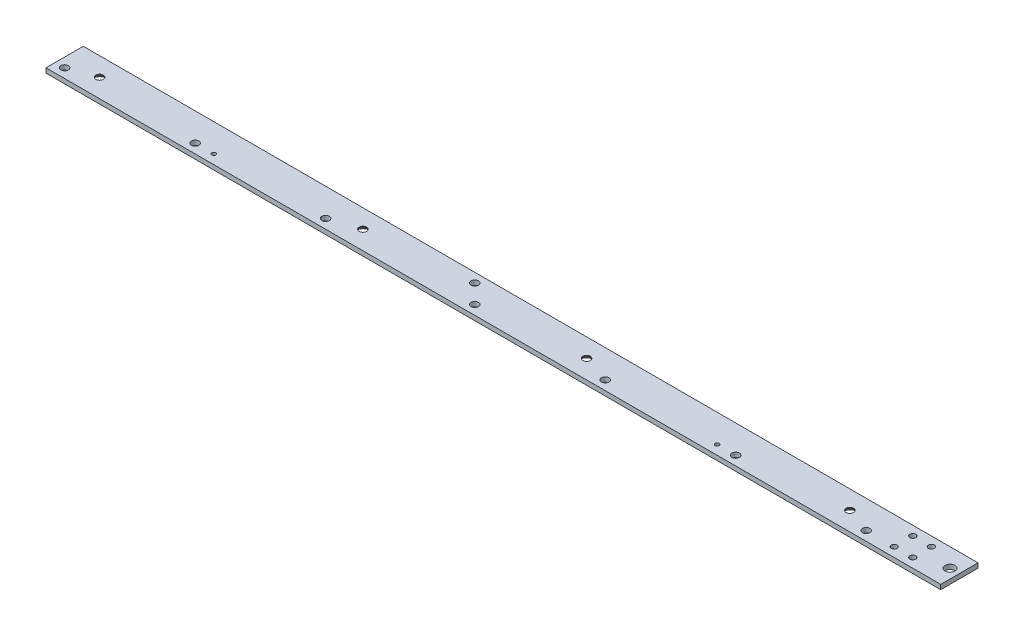
SolidWorks part; units mm, degrees
material "Copper"
ref_plane "Front Plane" through (0, 0, 0) normal (0, 0, 1) x (1, 0, 0)
ref_plane "Top Plane" through (0, 0, 0) normal (0, 1, 0) x (1, 0, 0)
ref_plane "Right Plane" through (0, 0, 0) normal (1, 0, 0) x (0, 0, -1)
sketch "Sketch1" plane through (0, 0, 0) normal (1, 0, 0) x (0, 0, -1)
  line L1 (-12.7, 1.5875) -> (12.7, 1.5875)
  line L2 (-12.7, 1.5875) -> (-12.7, -1.5875)
  line L3 (-12.7, -1.5875) -> (12.7, -1.5875)
  line L4 (12.7, 1.5875) -> (12.7, -1.5875)
  line L5 (-12.7, 1.5875) -> (12.7, -1.5875) construction
  line L6 (-12.7, -1.5875) -> (12.7, 1.5875) construction
  point P0 (0, 0)
  dimension "D1" = 3.175
  dimension "D2" = 25.4
extrude "Boss-Extrude1" add sketch "Sketch1" along normal mid plane 558.8
hole_wizard "#10 Clearance Hole1" positions "Sketch2" profile "Sketch3" hole size "#10" standard "ANSI Inch" end condition through all
sketch "Sketch2" plane through (0, 1.5875, 0) normal (0, 1, 0) x (1, 0, 0)
  line L0 (279.4, -12.7) -> (-279.4, -12.7) construction
  line L1 (-279.4, 12.7) -> (-279.4, -12.7) construction
  point P0 (-273.05, -6.35)
  point P2 (-184.15, -6.35)
  point P4 (-95.25, -6.35)
  dimension "D1" = 6.35
  dimension "D2" = 88.9
  dimension "D3" = 88.9
  dimension "D4" = 6.35
sketch "Sketch3" plane through (-273.05, 1.5875, 6.35) normal (1, 0, 0) x (0, 0, 1)
  line L0 (0, 0) -> (0, 3.175)
  line L1 (0, 3.175) -> (2.5527, 3.175)
  line L2 (2.5527, 3.175) -> (2.5527, 0)
  line L5 (2.5527, 0) -> (0, 0)
  line L11 (0, -6.35) -> (0, 107.95) construction
  dimension "Thru Hole Dia." = 5.1054
  dimension "Thru Hole Depth" = 3.175
hole_wizard "CSK for #10 Flat Head Machine Screw1" positions "Sketch4" profile "Sketch5" countersink size "#10" standard "ANSI Inch" end condition through all
sketch "Sketch4" plane through (0, -1.5875, 0) normal (0, -1, 0) x (-1, 0, 0)
  circle A0 centre (273.05, -6.35) radius 2.5527 construction
  circle A1 centre (95.25, -6.35) radius 2.5527 construction
  point P0 (255.5875, 0)
  point P2 (76.2, 0)
  dimension "D2" = 19.05
  dimension "D1" = 17.4625
sketch "Sketch5" plane through (-255.5875, -1.5875, 0) normal (1, 0, 0) x (0, 0, -1)
  line L0 (0, 0) -> (0, 3.175)
  line L1 (0, 3.175) -> (2.5527, 3.175)
  line L2 (2.5527, 3.175) -> (2.5527, 2.6882)
  line L3 (2.5527, 2.6882) -> (4.8895, 0)
  line L5 (4.8895, 0) -> (0, 0)
  line L6 (-2.5527, 2.6882) -> (-4.8895, 0) construction
  line L11 (0, -6.35) -> (0, 107.95) construction
  dimension "Thru Hole Dia." = 5.1054
  dimension "Thru Hole Depth" = 3.175
  dimension "Near C'Sink Dia." = 9.779
  dimension "Near C'Sink Angle" = 82
hole_wizard "#6-32 Tapped Hole1" positions "Sketch8" profile "Sketch9" tap size "#6-32" standard "ANSI Inch" end condition through all
sketch "Sketch8" plane through (0, 1.5875, 0) normal (0, 1, 0) x (1, 0, 0)
  line L0 (279.4, -12.7) -> (-279.4, -12.7) construction
  circle A0 centre (-184.15, -6.35) radius 2.5527 construction
  point P0 (-171.45, -6.35)
  dimension "D1" = 6.35
  dimension "D2" = 12.7
sketch "Sketch9" plane through (-171.45, 1.5875, 6.35) normal (1, 0, 0) x (0, 0, 1)
  line L0 (0, 0) -> (0, 3.175)
  line L1 (0, 3.175) -> (1.3525, 3.175)
  line L2 (1.3525, 3.175) -> (1.3525, 0)
  line L5 (1.3525, 0) -> (0, 0)
  line L11 (0, -6.35) -> (0, 107.95) construction
  dimension "Thru Tap Drill Dia." = 2.7051
  dimension "Thru Tap Drill Depth" = 3.175
cosmetic thread "Hole Thread1" parameters "D2"=3.5052
mirror "Mirror1" about plane through (0, 0, 0) normal (1, 0, 0) of "#6-32 Tapped Hole1", "#10 Clearance Hole1", "CSK for #10 Flat Head Machine Screw1"
hole_wizard "#10 Clearance Hole2" positions "Sketch10" profile "Sketch11" hole size "#10" standard "ANSI Inch" end condition through all
sketch "Sketch10" plane through (0, 1.5875, 0) normal (0, 1, 0) x (1, 0, 0)
  point P0 (-6.35, 6.35)
  point P2 (6.35, -6.35)
  dimension "D1" = 6.35
  dimension "D2" = 6.35
  dimension "D3" = 6.35
  dimension "D4" = 6.35
sketch "Sketch11" plane through (-6.35, 1.5875, -6.35) normal (1, 0, 0) x (0, 0, 1)
  line L0 (0, 0) -> (0, 3.175)
  line L1 (0, 3.175) -> (2.5527, 3.175)
  line L2 (2.5527, 3.175) -> (2.5527, 0)
  line L5 (2.5527, 0) -> (0, 0)
  line L11 (0, -6.35) -> (0, 107.95) construction
  dimension "Thru Hole Dia." = 5.1054
  dimension "Thru Hole Depth" = 3.175
sketch "Sketch12" plane through (279.4, 0, 0) normal (1, 0, 0) x (0, 0, -1)
  line L0 (-12.7, 1.5875) -> (-12.7, -1.5875) construction
  line L1 (-12.7, -1.5875) -> (12.7, -1.5875) construction
  line L2 (12.7, -1.5875) -> (12.7, 1.5875) construction
  line L3 (12.7, 1.5875) -> (-12.7, 1.5875) construction
  line L4 (-12.7, 1.5875) -> (-12.7, -1.5875)
  line L5 (-12.7, -1.5875) -> (12.7, -1.5875)
  line L6 (12.7, -1.5875) -> (12.7, 1.5875)
  line L7 (12.7, 1.5875) -> (-12.7, 1.5875)
extrude "Boss-Extrude2" add sketch "Sketch12" along normal blind 50.8
hole_wizard "1/4 Clearance Hole1" positions "Sketch13" profile "Sketch14" hole size "1/4" standard "ANSI Inch" end condition through all
sketch "Sketch13" plane through (0, 1.5875, 0) normal (0, 1, 0) x (1, 0, 0)
  line L0 (330.2, 12.7) -> (330.2, -12.7) construction
  point P0 (323.85, 0)
  dimension "D1" = 6.35
sketch "Sketch14" plane through (323.85, 1.5875, 0) normal (1, 0, 0) x (0, 0, 1)
  line L0 (0, 0) -> (0, 3.175)
  line L1 (0, 3.175) -> (3.3782, 3.175)
  line L2 (3.3782, 3.175) -> (3.3782, 0)
  line L5 (3.3782, 0) -> (0, 0)
  line L11 (0, -6.35) -> (0, 107.95) construction
  dimension "Thru Hole Dia." = 6.7564
  dimension "Thru Hole Depth" = 3.175
hole_wizard "#10-32 Tapped Hole1" positions "Sketch15" profile "Sketch16" tap size "#10-32" standard "ANSI Inch" end condition through all
sketch "Sketch15" plane through (0, 1.5875, 0) normal (0, 1, 0) x (1, 0, 0)
  line L0 (330.2, 12.7) -> (-279.4, 12.7) construction
  circle A0 centre (323.85, 0) radius 3.3782 construction
  point P0 (304.8, 6.35)
  point P2 (292.1, 6.35)
  point P4 (304.8, -6.35)
  point P6 (292.1, -6.35)
  point P9 (0, 0)
  point P10 (0, 0)
  point P11 (0, 0)
  point P12 (0, 0)
  dimension "D1" = 12.7
  dimension "D2" = 12.7
  dimension "D3" = 6.35
  dimension "D4" = 19.05
sketch "Sketch16" plane through (304.8, 1.5875, -6.35) normal (1, 0, 0) x (0, 0, 1)
  line L0 (0, 0) -> (0, 3.175)
  line L1 (0, 3.175) -> (2.0193, 3.175)
  line L2 (2.0193, 3.175) -> (2.0193, 0)
  line L5 (2.0193, 0) -> (0, 0)
  line L11 (0, -6.35) -> (0, 107.95) construction
  dimension "Thru Tap Drill Dia." = 4.0386
  dimension "Thru Tap Drill Depth" = 3.175
cosmetic thread "Hole Thread2" parameters "D2"=4.826
cosmetic thread "Hole Thread3" parameters "D2"=4.826
cosmetic thread "Hole Thread4" parameters "D2"=4.826
cosmetic thread "Hole Thread5" parameters "D2"=4.826
